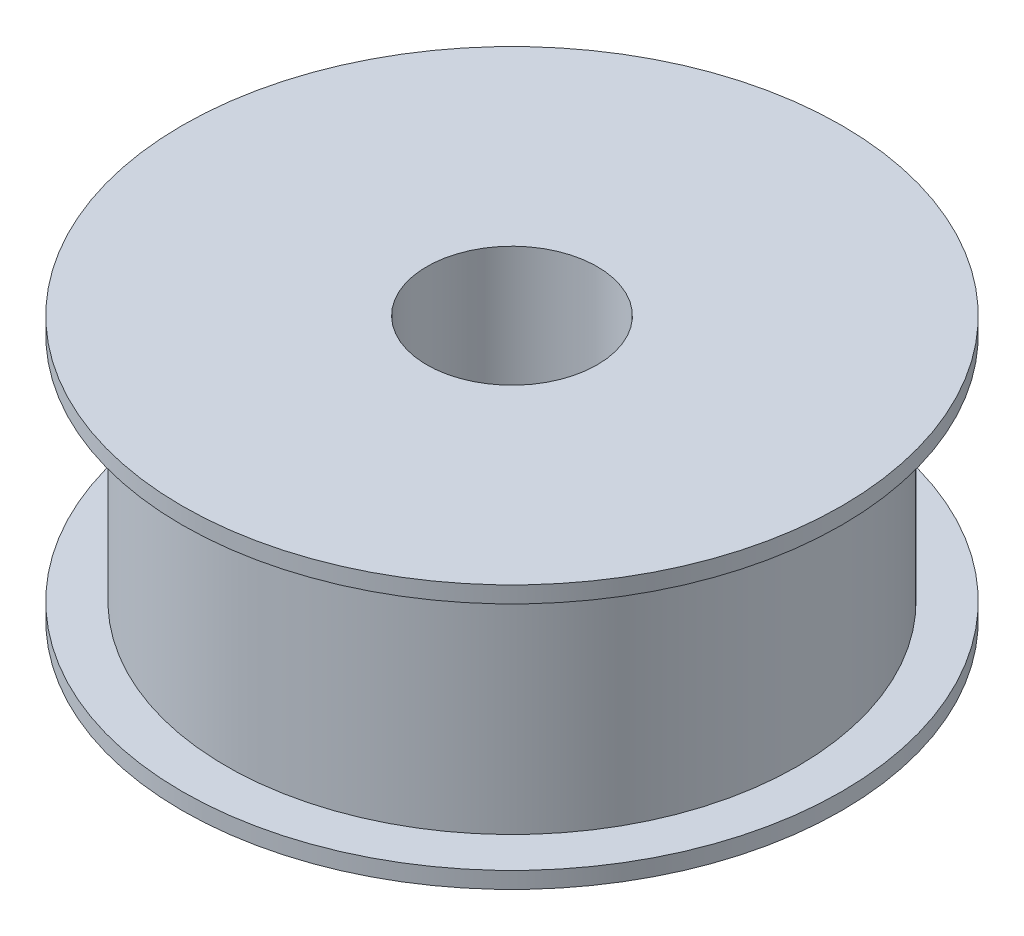
SolidWorks part; units mm, degrees
ref_plane "Front Plane" through (0, 0, 0) normal (0, 0, 1) x (1, 0, 0)
ref_plane "Top Plane" through (0, 0, 0) normal (0, 1, 0) x (1, 0, 0)
ref_plane "Right Plane" through (0, 0, 0) normal (1, 0, 0) x (0, 0, -1)
sketch "Sketch1" plane through (0, 0, 0) normal (0, 0, 1) x (1, 0, 0)
  line L0 (0, -523.101) -> (0, 25631.9477) construction
  line L1 (-523.101, 0) -> (25631.9477, 0) construction
  line L2 (15.5, 24) -> (60, 24)
  line L3 (60, 24) -> (60, 21)
  line L4 (60, 21) -> (52, 21)
  line L5 (60, -21) -> (52, -21)
  line L6 (60, -24) -> (60, -21)
  line L7 (15.5, -24) -> (60, -24)
  line L8 (52, -21) -> (52, 21)
  line L9 (15.5, 24) -> (15.5, -24)
  dimension "D1" = 48
  dimension "D2" = 120
  dimension "D3" = 31
  dimension "D4" = 3
  dimension "D5" = 8
revolve "Revolve1" add sketch "Sketch1" angle 360 about L0
